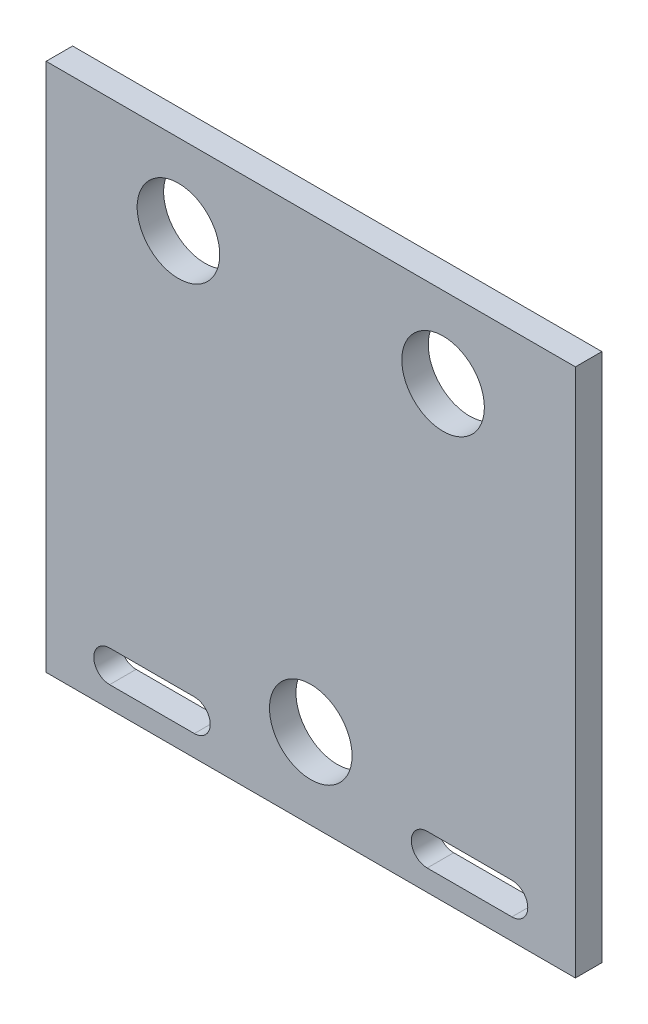
SolidWorks part; units mm, degrees
ref_plane "Front Plane" through (0, 0, 0) normal (0, 0, 1) x (1, 0, 0)
ref_plane "Top Plane" through (0, 0, 0) normal (0, 1, 0) x (1, 0, 0)
ref_plane "Right Plane" through (0, 0, 0) normal (1, 0, 0) x (0, 0, -1)
sketch "Sketch1" plane through (0, 0, 0) normal (0, 0, 1) x (1, 0, 0)
  line L0 (-15.875, 22.065) -> (15.875, 22.065) construction
  line L1 (-31.75, 31.75) -> (31.75, 31.75)
  line L2 (-31.75, 31.75) -> (-31.75, -31.75)
  line L3 (-31.75, -31.75) -> (31.75, -31.75)
  line L4 (31.75, 31.75) -> (31.75, -31.75)
  line L5 (0, 22.065) -> (0, -22.065) construction
  line L6 (13.97, -27.305) -> (24.13, -27.305) construction
  line L7 (13.97, -25.4) -> (24.13, -25.4)
  line L8 (13.97, -29.21) -> (24.13, -29.21)
  line L9 (-13.97, -27.305) -> (-24.13, -27.305) construction
  line L10 (-13.97, -25.4) -> (-24.13, -25.4)
  line L11 (-13.97, -29.21) -> (-24.13, -29.21)
  circle A0 centre (-15.875, 22.065) radius 4.953
  circle A1 centre (15.875, 22.065) radius 4.953
  circle A2 centre (0, -22.065) radius 4.953
  arc A3 (13.97, -25.4) -> (13.97, -29.21) centre (13.97, -27.305) ccw
  arc A4 (24.13, -29.21) -> (24.13, -25.4) centre (24.13, -27.305) ccw
  arc A5 (-13.97, -25.4) -> (-13.97, -29.21) centre (-13.97, -27.305) cw
  arc A6 (-24.13, -29.21) -> (-24.13, -25.4) centre (-24.13, -27.305) cw
  point P4 (0, 31.75)
  point P6 (-31.75, 0)
  point P13 (0, 22.065)
  point P15 (0, 0)
  point P18 (19.05, -27.305)
  point P23 (19.05, -27.4749)
  point P24 (19.05, -25.3012)
  point P27 (-19.05, -27.305)
  dimension "D3" = 44.13
  dimension "D5" = 9.906
  dimension "D6" = 9.906
  dimension "D7" = 9.906
  dimension "D9" = 12.7
  dimension "D1" = 63.5
  dimension "D2" = 63.5
  dimension "D4" = 31.75
  dimension "D8" = 3.81
  dimension "D10" = 10.16
  dimension "D11" = 2.54
extrude "Boss-Extrude1" add sketch "Sketch1" along normal blind 3.175
